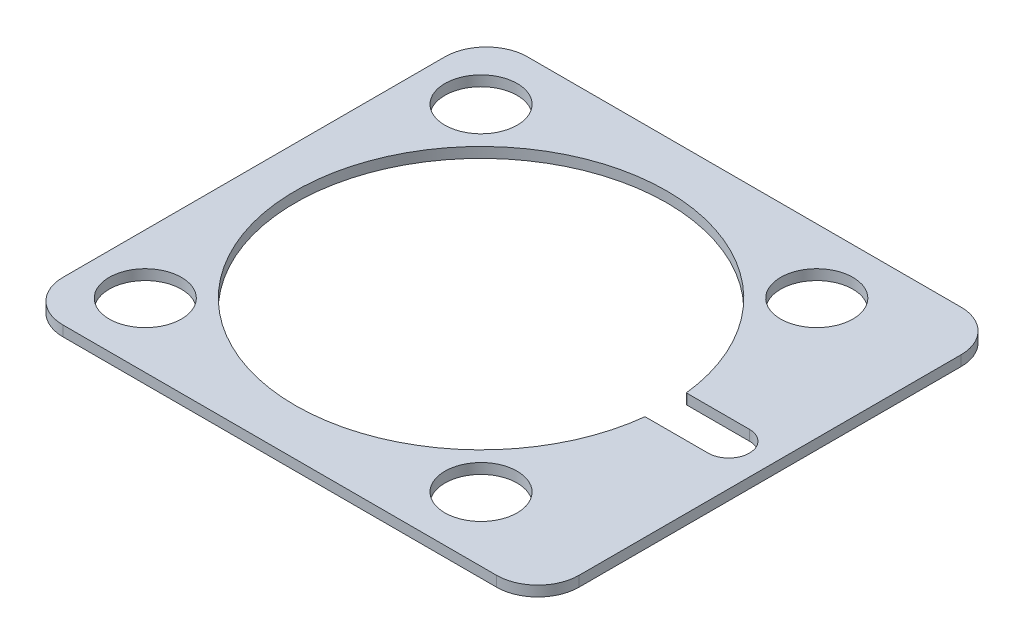
SolidWorks part; units mm, degrees
material "Rubber"
ref_plane "Front Plane" through (0, 0, 0) normal (0, 0, 1) x (1, 0, 0)
ref_plane "Top Plane" through (0, 0, 0) normal (0, 1, 0) x (1, 0, 0)
ref_plane "Right Plane" through (0, 0, 0) normal (1, 0, 0) x (0, 0, -1)
sketch "Sketch1" plane through (0, 0, 0) normal (0, 1, 0) x (1, 0, 0)
  line L0 (-35.6489, 0) -> (47.526, 0) construction
  line L5 (-21, -22.5) -> (21, -22.5)
  line L6 (-25, -18.5) -> (-25, 18.5)
  line L7 (-21, 22.5) -> (21, 22.5)
  line L8 (25, -18.5) -> (25, 18.5)
  line L11 (-25, -22.5) -> (25, 22.5) construction
  line L12 (-25, 22.5) -> (25, -22.5) construction
  line L13 (-3, 27.1873) -> (-3, -28.2626) construction
  line L14 (-3, 0) -> (-35.5269, 32.5269) construction
  line L15 (15, 0) -> (21, 0) construction
  line L16 (15, 2) -> (21, 2)
  line L17 (15, -2) -> (21, -2)
  arc A13 (15, 2) -> (14.8889, 1.9969) centre (15, 0) ccw
  arc A14 (-21, -22.5) -> (-25, -18.5) centre (-21, -18.5) cw
  arc A15 (21, -22.5) -> (25, -18.5) centre (21, -18.5) ccw
  arc A16 (21, 22.5) -> (25, 18.5) centre (21, 18.5) cw
  arc A17 (-25, 18.5) -> (-21, 22.5) centre (-21, 18.5) cw
  circle A18 centre (-3, 0) radius 23 construction
  circle A20 centre (-19.2635, 16.2635) radius 3.5
  circle A21 centre (13.2635, 16.2635) radius 3.5
  circle A22 centre (13.2635, -16.2635) radius 3.5
  circle A23 centre (-19.2635, -16.2635) radius 3.5
  arc A24 (14.8889, 1.9969) -> (14.8889, -1.9969) centre (-3, 0) ccw
  arc A25 (21, -2) -> (21, 2) centre (21, 0) ccw
  arc A26 (14.8889, -1.9969) -> (15, -2) centre (15, 0) ccw
  point P0 (0, 0)
  point P26 (0, 0)
  point P35 (-3, 0)
  point P36 (18, 0)
  point P41 (18, -2)
  point P42 (0, 0)
  dimension "D3" = 4
  dimension "D5" = 46
  dimension "D6" = 45
  dimension "D11" = 36
  dimension "D16" = 2
  dimension "D7" = 7
  dimension "D9" = 23
  dimension "D1" = 45
  dimension "D2" = 50
  dimension "D4" = 22
  dimension "D8" = 23
  dimension "D10" = 16.2635
  dimension "D12" = 24
  dimension "D13" = 4
  dimension "D14" = 6
  dimension "D15" = 6
  dimension "D17" = 2
  dimension "D18" = 2
  dimension "D19" = 3
  dimension "D20" = 3
  dimension "D21" = 18
extrude "Boss-Extrude1" add sketch "Sketch1" along normal blind 1
